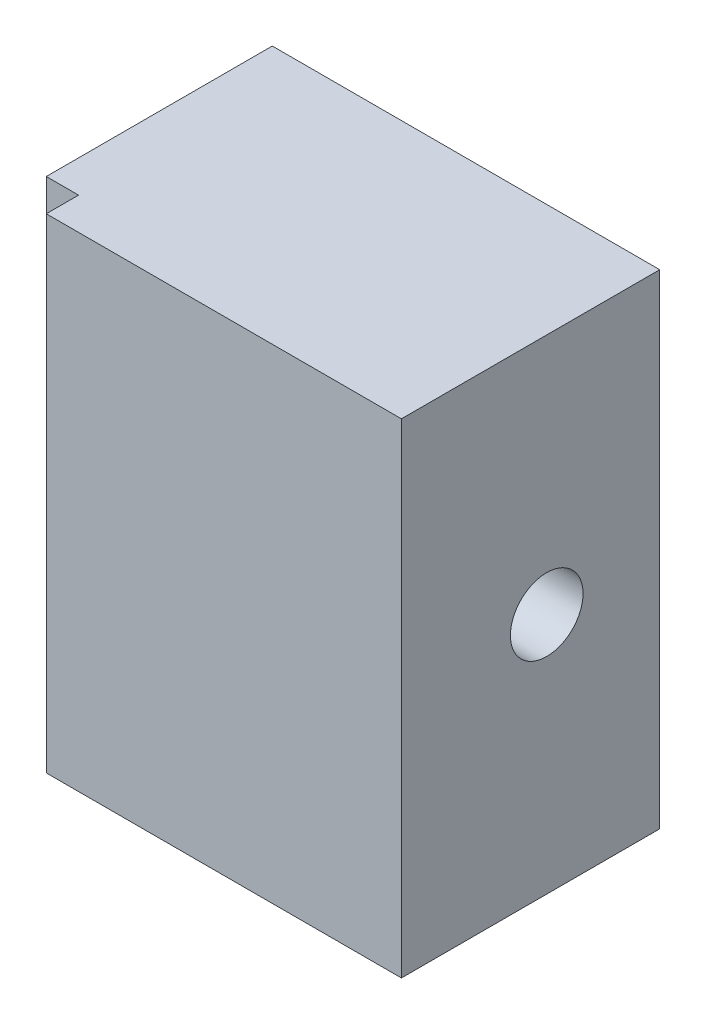
SolidWorks part; units mm, degrees
material "Plain Carbon Steel"
ref_plane "Front Plane" through (0, 0, 0) normal (0, 0, 1) x (1, 0, 0)
ref_plane "Top Plane" through (0, 0, 0) normal (0, 1, 0) x (1, 0, 0)
ref_plane "Right Plane" through (0, 0, 0) normal (1, 0, 0) x (0, 0, -1)
sketch "Sketch1" plane through (0, 0, 0) normal (1, 0, 0) x (0, 0, -1)
  line L1 (0, 0) -> (-16, 0)
  line L2 (0, 0) -> (0, 30)
  line L3 (0, 30) -> (-16, 30)
  line L4 (-16, 0) -> (-16, 30)
  dimension "D1" = 30
  dimension "D2" = 16
extrude "Boss-Extrude1" add sketch "Sketch1" along normal blind 24
sketch "Sketch2" plane through (0, 0, 0) normal (-1, 0, 0) x (0, 0, 1)
  line L6 (16, 30) -> (14, 30)
  line L7 (16, 30) -> (16, 0)
  line L8 (16, 0) -> (14, 0)
  line L9 (14, 30) -> (14, 0)
  dimension "D2" = 2
extrude "Cut-Extrude1" cut sketch "Sketch2" against normal blind 2
hole_wizard "M4 Clearance Hole1" positions "Sketch4" profile "Sketch5" hole size "M4" standard "ISO" end condition through all
sketch "Sketch4" plane through (24, 0, 0) normal (1, 0, 0) x (0, 0, -1)
  line L0 (0, 30) -> (-16, 30) construction
  line L2 (0, 0) -> (0, 30) construction
  point P0 (-7, 15)
  dimension "D1" = 15
  dimension "D2" = 7
sketch "Sketch5" plane through (24, 15, 7) normal (0, 1, 0) x (0, 0, -1)
  line L0 (0, 0) -> (0, 24)
  line L1 (0, 24) -> (2.25, 24)
  line L2 (2.25, 24) -> (2.25, 0)
  line L5 (2.25, 0) -> (0, 0)
  line L11 (0, -6.35) -> (0, 107.95) construction
  dimension "Thru Hole Dia." = 4.5
  dimension "Thru Hole Depth" = 24
